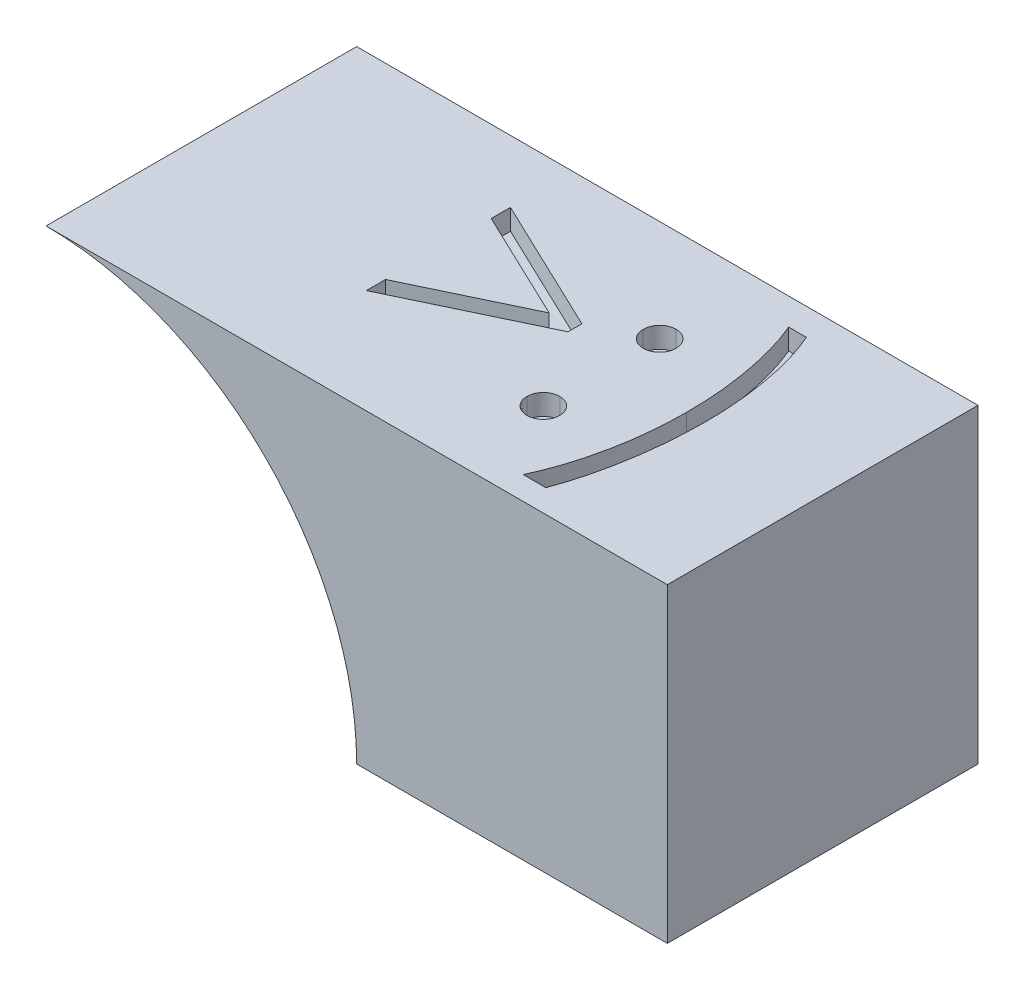
SolidWorks part; units mm, degrees
ref_plane "Front Plane" through (0, 0, 0) normal (0, 0, 1) x (1, 0, 0)
ref_plane "Top Plane" through (0, 0, 0) normal (0, 1, 0) x (1, 0, 0)
ref_plane "Right Plane" through (0, 0, 0) normal (1, 0, 0) x (0, 0, -1)
sketch "Sketch1" plane through (0, 0, 0) normal (0, 1, 0) x (1, 0, 0)
  line L1 (-15, -7.5) -> (15, -7.5)
  line L2 (-15, -7.5) -> (-15, 7.5)
  line L3 (-15, 7.5) -> (15, 7.5)
  line L4 (15, -7.5) -> (15, 7.5)
  line L5 (-15, -7.5) -> (15, 7.5) construction
  line L6 (-15, 7.5) -> (15, -7.5) construction
  point P0 (0, 0)
  dimension "D1" = 30
  dimension "D2" = 15
extrude "Boss-Extrude1" add sketch "Sketch1" along normal blind 15
sketch "Sketch2" plane through (0, 0, 7.5) normal (0, 0, 1) x (1, 0, 0)
  circle A0 centre (-15, 0) radius 15
extrude "Cut-Extrude1" cut sketch "Sketch2" against normal blind 15
sketch "Sketch3" plane through (0, 15, 0) normal (0, 1, 0) x (1, 0, 0)
  line L0 (-5.2979, -3.691) -> (14.4123, -3.691) construction
  text T0 ">:)" font "Century Gothic" height in points 36
  point P3 (-7.7083, -4.1931)
  point P4 (-7.2062, -4.1429)
  point P5 (-6.3274, -3.8667)
  point P6 (-5.8252, -3.8416)
  point P7 (0, 0)
  point P8 (0, 0)
  point P9 (-5.2979, -3.691)
extrude "Cut-Extrude2" cut sketch "Sketch3" against normal blind 1
